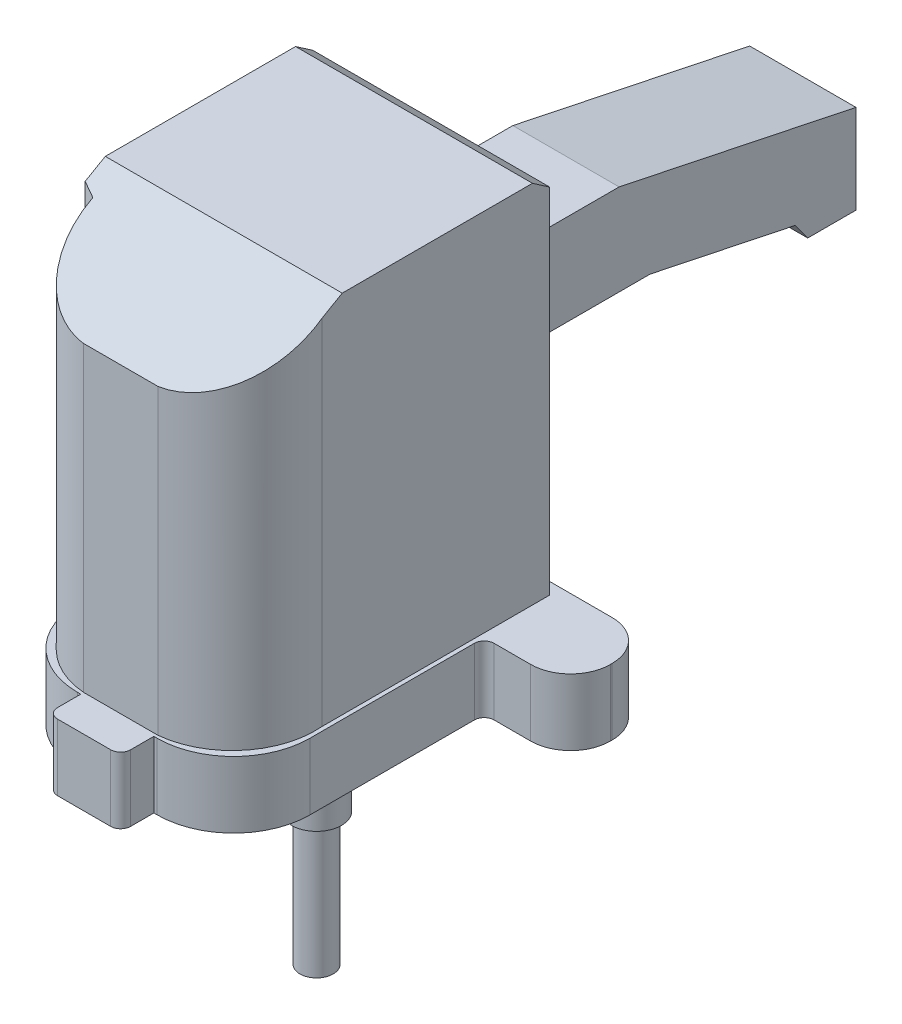
SolidWorks part; units mm, degrees
ref_plane "Спереди" through (0, 0, 0) normal (0, 0, 1) x (1, 0, 0)
ref_plane "Сверху" through (0, 0, 0) normal (0, 1, 0) x (1, 0, 0)
ref_plane "Справа" through (0, 0, 0) normal (1, 0, 0) x (0, 0, -1)
sketch "Эскиз1" plane through (0, 0, 0) normal (0, 1, 0) x (1, 0, 0)
  line L0 (35, 12.5) -> (35, -37)
  line L1 (-49, 40) -> (49, 40)
  line L3 (-8, -70) -> (8, -70)
  line L6 (-40, -32) -> (-40, 12.5)
  line L7 (-37, -35) -> (-35, -35)
  line L8 (38, 15.5) -> (49, 15.5)
  line L9 (61, 27.5) -> (61, 28)
  line L10 (-61, 28) -> (-61, 27.5)
  line L11 (-49, 15.5) -> (-43, 15.5)
  line L12 (-35, -35) -> (-35, -37)
  line L13 (-12, -60) -> (-11, -60)
  line L14 (-11, -60) -> (-11, -67)
  line L15 (11, -67) -> (11, -60)
  line L16 (11, -60) -> (12, -60)
  circle A0 centre (27.5, 27.5) radius 2
  circle A1 centre (-27.5, 27.5) radius 2
  circle A2 centre (-27.5, -27.5) radius 2
  circle A3 centre (27.5, -27.5) radius 2
  circle A4 centre (0, 0) radius 10
  arc A5 (49, 15.5) -> (61, 27.5) centre (49, 27.5) ccw
  arc A6 (-61, 27.5) -> (-49, 15.5) centre (-49, 27.5) ccw
  arc A7 (-49, 40) -> (-61, 28) centre (-49, 28) ccw
  arc A8 (61, 28) -> (49, 40) centre (49, 28) ccw
  arc A9 (-40, -32) -> (-37, -35) centre (-37, -32) ccw
  arc A10 (38, 15.5) -> (35, 12.5) centre (38, 12.5) ccw
  arc A11 (-40, 12.5) -> (-43, 15.5) centre (-43, 12.5) ccw
  arc A14 (-35, -37) -> (-12, -60) centre (-12, -37) ccw
  arc A15 (12, -60) -> (35, -37) centre (12, -37) ccw
  arc A16 (8, -70) -> (11, -67) centre (8, -67) ccw
  arc A17 (-8, -70) -> (-11, -67) centre (-8, -67) cw
  point P30 (-40, -35)
  dimension "D3" = 12
  dimension "D4" = 3
  dimension "D5" = 23
  dimension "D6" = 3
  dimension "D1" = 2
  dimension "D2" = 2
extrude "Бобышка-Вытянуть1" add sketch "Эскиз1" along normal blind 20
sketch "Эскиз2" plane through (0, 0, 0) normal (0, -1, 0) x (1, 0, 0)
  circle A0 centre (0, 0) radius 25
  circle A1 centre (0, 0) radius 12
extrude "Бобышка-Вытянуть2" add sketch "Эскиз2" along normal blind 2
sketch "Эскиз3" plane through (0, 20, 0) normal (0, 1, 0) x (1, 0, 0)
  line L0 (-37.5837, -32.1035) -> (-37.5837, 36.4574)
  line L1 (-37.5837, 36.4574) -> (-16, 36.4574)
  line L2 (33.7666, 36.4574) -> (33.7666, -32.1035)
  line L3 (-37.5837, -32.1035) -> (-33.3262, -34.0483)
  line L4 (-11, -59.1168) -> (11.3045, -59.1168)
  line L6 (16, 36.4574) -> (33.7666, 36.4574)
  line L7 (-16, 36.4574) -> (-16, 146.4574)
  line L8 (-16, 146.4574) -> (16, 146.4574)
  line L9 (16, 146.4574) -> (16, 36.4574)
  arc A0 (33.7666, -32.1035) -> (11.3045, -59.1168) centre (8.8578, -34.2369) cw
  arc A1 (-33.3262, -34.0483) -> (-11, -59.1168) centre (-9.2191, -35.0546) ccw
extrude "Бобышка-Вытянуть3" add sketch "Эскиз3" along normal blind 110
sketch "Эскиз4" plane through (0, 0, 0) normal (1, 0, 0) x (0, 0, -1)
  line L0 (-59.1168, 111.0091) -> (-59.1168, 20)
  line L1 (-59.1168, 130) -> (-59.1168, 20) construction
  line L3 (36.4574, 20) -> (36.4574, 70.8265)
  line L4 (36.4574, 130) -> (36.4574, 20) construction
  line L5 (36.4574, 70.8265) -> (84.4124, 70.8265)
  line L6 (84.4124, 70.8265) -> (128.1932, 61.6738)
  line L7 (128.1932, 61.6738) -> (131.9337, 56.4999)
  line L8 (131.9337, 56.4999) -> (146.4574, 56.4999)
  line L9 (146.4574, 130) -> (146.4574, 20) construction
  line L10 (146.4574, 56.4999) -> (146.4574, 83.3278)
  line L11 (146.4574, 83.3278) -> (75.1219, 98.241)
  line L12 (75.1219, 98.241) -> (43.3924, 98.241)
  line L13 (43.3924, 98.241) -> (36.4574, 102.0797)
  line L14 (36.4574, 130) -> (36.4574, 20) construction
  line L15 (36.4574, 102.0797) -> (36.4574, 126.416)
  line L16 (36.4574, 126.416) -> (31.2624, 130)
  line L17 (-32.1035, 130) -> (36.4574, 130) construction
  line L18 (31.2624, 130) -> (-26.0369, 130)
  line L19 (-26.0369, 130) -> (-59.1168, 111.0091)
  line L21 (36.4574, 20) -> (40, 20)
  line L22 (40, 20) -> (40, 0)
  line L23 (40, 0) -> (25.5, 0)
  line L24 (25.5, 0) -> (25.5, -2.4657)
  line L25 (25.5, -2.4657) -> (-25.617, -2.4657)
  line L26 (-25.617, -2.4657) -> (-25.617, 0)
  line L27 (-37, 0) -> (12.5, 0) construction
  line L28 (-25.617, 0) -> (-70, 0)
  line L29 (-70, 20) -> (-70, 0) construction
  line L30 (-70, 0) -> (-67, 0) construction
  line L31 (-70, 0) -> (-70, 20)
  line L32 (-70, 20) -> (-59.1168, 20)
extrude "Вырез-Вытянуть5" cut sketch "Эскиз4" against normal through all both and the other way through all flip side to cut
sketch "Эскиз5" plane through (0, 20, 0) normal (0, -1, 0) x (1, 0, 0)
  circle A0 centre (0, 0) radius 7.5
extrude "Бобышка-Вытянуть4" add sketch "Эскиз5" along normal blind 55
sketch "Эскиз6" plane through (0, -35, 0) normal (0, -1, 0) x (1, 0, 0)
  circle A0 centre (0, 0) radius 5
extrude "Бобышка-Вытянуть5" add sketch "Эскиз6" along normal blind 40
